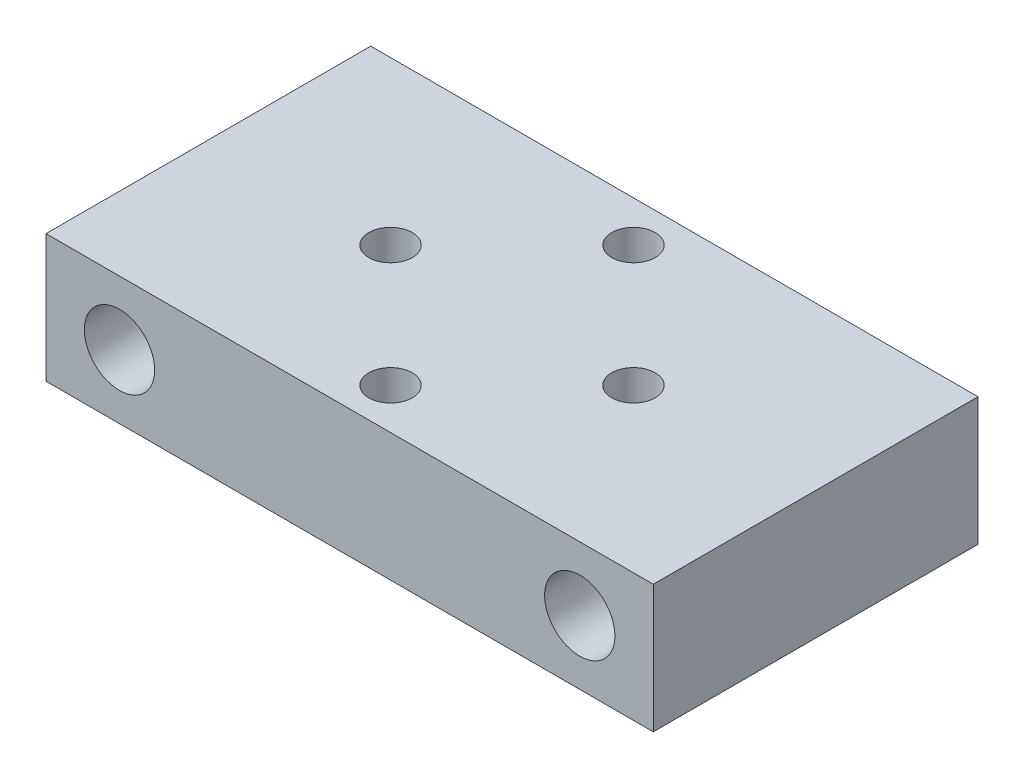
SolidWorks part; units mm, degrees
material "1060 Alloy"
ref_plane "Front Plane" through (0, 0, 0) normal (0, 0, 1) x (1, 0, 0)
ref_plane "Top Plane" through (0, 0, 0) normal (0, 1, 0) x (1, 0, 0)
ref_plane "Right Plane" through (0, 0, 0) normal (1, 0, 0) x (0, 0, -1)
sketch "Sketch1" plane through (0, 0, 0) normal (0, 1, 0) x (1, 0, 0)
  line L0 (0, 9.5) -> (0, 0) construction
  line L1 (0, 0) -> (9.5, 0) construction
  line L2 (0, -1000) -> (0, 49000) construction
  line L3 (-23.75, 12.7) -> (-15.25, 12.7)
  line L6 (-20.75, 12.7) -> (-20.75, -12.7) construction
  line L8 (-23.75, 12.7) -> (-23.75, -12.7)
  line L9 (-23.75, -12.7) -> (-15.25, -12.7)
  line L10 (-15.25, 12.7) -> (-15.25, -12.7) construction
  line L11 (-15.25, 12.7) -> (15.25, 12.7)
  line L12 (-15.25, -12.7) -> (15.25, -12.7)
  line L13 (15.25, 12.7) -> (15.25, -12.7) construction
  line L14 (20.75, 12.7) -> (20.75, -12.7) construction
  line L15 (23.75, -12.7) -> (15.25, -12.7)
  line L16 (23.75, 12.7) -> (23.75, -12.7)
  line L17 (23.75, 12.7) -> (15.25, 12.7)
  circle A0 centre (-9.5, 0) radius 2.75 construction
  circle A1 centre (9.5, 0) radius 2.75 construction
  point P5 (0, 9.5)
  point P6 (9.5, 0)
  point P7 (0, -9.5)
  point P8 (-9.5, 0)
  point P12 (0, 12.7)
  point P21 (-23.75, 0)
  point P27 (0, 12.7)
  point P28 (-20.75, 0)
  point P29 (20.75, 0)
  point P33 (0, -12.7)
  dimension "D2" = 25.4
  dimension "D4" = 5.5
  dimension "D5" = 5.5
  dimension "D6" = 3
  dimension "D1" = 19
  dimension "D3" = 3
extrude "Boss-Extrude1" add sketch "Sketch1" against normal mid plane 10
hole_wizard "CSK for M3 Flat Head Machine Screw1" positions "Sketch4" profile "Sketch6" countersink size "M3" standard "ANSI Metric" end condition through all
sketch "Sketch4" plane through (0, -5, 0) normal (0, -1, 0) x (-1, 0, 0)
  point P0 (-9.5, 0)
  point P3 (0, 9.5)
  point P6 (9.5, 0)
  point P9 (0, -9.5)
sketch "Sketch6" plane through (9.5, -5, 0) normal (1, 0, 0) x (0, 0, -1)
  line L0 (0, 0) -> (0, 10)
  line L1 (0, 10) -> (1.7, 10)
  line L2 (1.7, 10) -> (1.7, 1.45)
  line L3 (1.7, 1.45) -> (3.15, 0)
  line L5 (3.15, 0) -> (0, 0)
  line L6 (-1.7, 1.45) -> (-3.15, 0) construction
  line L11 (0, -6.35) -> (0, 107.95) construction
  dimension "Thru Hole Dia." = 3.4
  dimension "Thru Hole Depth" = 10
  dimension "Near C'Sink Dia." = 6.3
  dimension "Near C'Sink Angle" = 90
sketch "Sketch7" plane through (0, 0, 12.7) normal (0, 0, 1) x (1, 0, 0)
  line L0 (-23.75, 0) -> (-15.25, 0) construction
  line L1 (0, -5.5) -> (0, 5.5) construction
  point P0 (-15.25, 0)
  point P1 (15.25, 0)
  point P3 (-18, 0)
  point P5 (0, 0)
  point P6 (0, 0)
  point P7 (0, 0)
  point P10 (0, 0)
  point P13 (18, 0)
  point P14 (0, 0)
  dimension "D1" = 2.75
hole_wizard "Ø5.5 (5.5) Diameter Hole1" positions "3DSketch2" profile "Sketch10" hole size "Ø5.5" standard "ANSI Metric"
sketch3d "3DSketch2"
  point P7 (-18, 0, 12.7)
  point P13 (18, 0, 12.7)
sketch "Sketch10" plane through (-18, 0, 12.7) normal (1, 0, 0) x (0, -1, 0)
  line L0 (0, 0) -> (0, 11.6524)
  line L1 (0, 11.6524) -> (2.75, 10)
  line L2 (2.75, 10) -> (2.75, 0)
  line L5 (2.75, 0) -> (0, 0)
  line L10 (0, 11.6524) -> (-2.75, 10) construction
  line L11 (0, -6.35) -> (0, 107.95) construction
  dimension "Hole Dia." = 5.5
  dimension "Hole Depth" = 10
  dimension "Drill Angle" = 118
mirror "Mirror1" about plane through (0, 0, 0) normal (0, 0, 1) of "Ø5.5 (5.5) Diameter Hole1"
